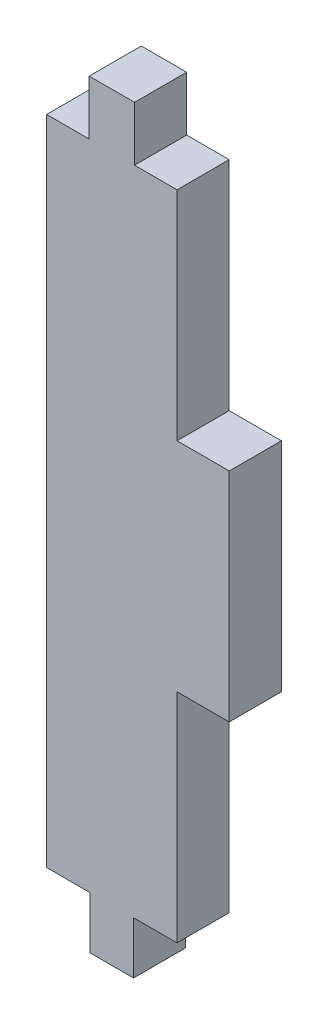
SolidWorks part; units mm, degrees
ref_plane "Front Plane" through (0, 0, 0) normal (0, 0, 1) x (1, 0, 0)
ref_plane "Top Plane" through (0, 0, 0) normal (0, 1, 0) x (1, 0, 0)
ref_plane "Right Plane" through (0, 0, 0) normal (1, 0, 0) x (0, 0, -1)
sketch "Sketch1" plane through (0, 0, 0) normal (0, 0, 1) x (1, 0, 0)
  line L0 (-33.9704, -12.0044) -> (-30.4908, -12.0044)
  line L1 (-37.2306, -16.18) -> (-27.2306, -16.18)
  line L2 (-37.2306, -16.18) -> (-37.2306, -66.18)
  line L3 (-37.2306, -66.18) -> (-27.2306, -66.18)
  line L4 (-27.2306, -16.18) -> (-27.2306, -66.18)
  line L5 (-37.2306, -16.18) -> (-27.2306, -66.18) construction
  line L6 (-37.2306, -66.18) -> (-27.2306, -16.18) construction
  line L7 (-33.8973, -62.18) -> (-30.5639, -62.18)
  line L8 (-33.8973, -62.18) -> (-33.8973, -70.18)
  line L9 (-33.8973, -70.18) -> (-30.5639, -70.18)
  line L10 (-30.5639, -62.18) -> (-30.5639, -70.18)
  line L11 (-33.8973, -62.18) -> (-30.5639, -70.18) construction
  line L12 (-33.8973, -70.18) -> (-30.5639, -62.18) construction
  line L13 (-33.9704, -12.0044) -> (-33.9704, -20.3556)
  line L14 (-33.9704, -20.3556) -> (-30.4908, -20.3556)
  line L15 (-30.4908, -12.0044) -> (-30.4908, -20.3556)
  line L16 (-33.9704, -12.0044) -> (-30.4908, -20.3556) construction
  line L17 (-33.9704, -20.3556) -> (-30.4908, -12.0044) construction
  line L19 (-27.2306, -49.5133) -> (-23.2306, -49.5133)
  line L20 (-27.2306, -49.5133) -> (-27.2306, -32.8467)
  line L21 (-27.2306, -32.8467) -> (-23.2306, -32.8467)
  line L22 (-23.2306, -49.5133) -> (-23.2306, -32.8467)
  point P0 (-32.2306, -41.18)
  point P5 (-32.2306, -66.18)
  point P10 (-32.2306, -16.18)
  dimension "D1" = 50
  dimension "D2" = 10
  dimension "D3" = 4
  dimension "D4" = 1.6667
  dimension "D5" = 16.6667
  dimension "D6" = 16.6667
  dimension "D7" = 4
extrude "Boss-Extrude1" add sketch "Sketch1" along normal blind 4 contours L1 L4 L3 L2 | L13 L14 L15 L0 | L10 L9 L8 L7 | L22 L21 L20 L19
equation "\"mat\"=\"mat@V1.assembly\""
equation "\"D3@Sketch1\"=\"mat\""
equation "\"D4@Sketch1\" = 10/6"
equation "\"D1@Boss-Extrude1\"=\"mat\""
equation "\"D7@Sketch1\" = \"mat\""
